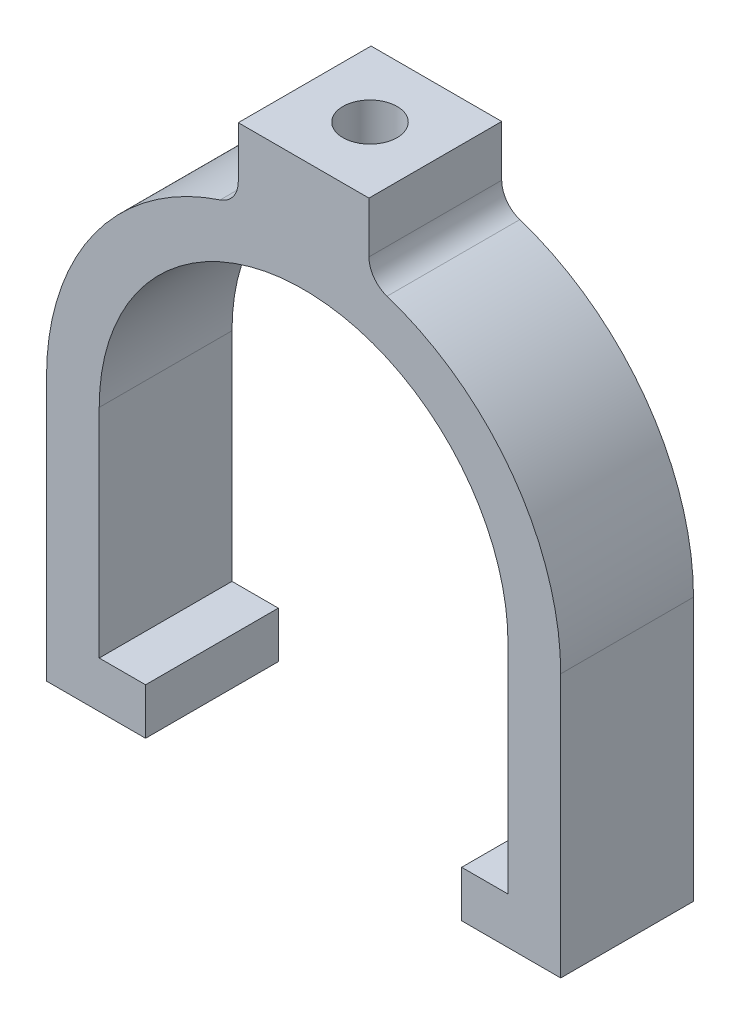
SolidWorks part; units mm, degrees
ref_plane "Front Plane" through (0, 0, 0) normal (0, 0, 1) x (1, 0, 0)
ref_plane "Top Plane" through (0, 0, 0) normal (0, 1, 0) x (1, 0, 0)
ref_plane "Right Plane" through (0, 0, 0) normal (1, 0, 0) x (0, 0, -1)
sketch "Sketch2" plane through (0, 0, 0) normal (0, 0, 1) x (1, 0, 0)
  line L0 (-24.6349, 0) -> (-24.6349, -26.162)
  line L1 (-24.6349, -26.162) -> (-19.05, -26.162)
  line L2 (-19.05, -26.162) -> (-19.05, -31.75)
  line L3 (-19.05, -31.75) -> (-30.988, -31.75)
  line L4 (-30.988, -31.75) -> (-30.988, 0)
  line L11 (24.6349, -26.162) -> (24.6349, 0)
  line L12 (-7.874, 38.1) -> (7.874, 38.1)
  line L13 (7.874, 38.1) -> (7.874, 29.5766)
  line L14 (24.6349, -26.162) -> (19.05, -26.162)
  line L15 (19.05, -26.162) -> (19.05, -31.75)
  line L16 (19.05, -31.75) -> (30.988, -31.75)
  line L18 (30.988, -31.75) -> (30.988, 0)
  line L19 (-7.874, 38.1) -> (-7.874, 29.5766)
  line L20 (0, 0) -> (0, 24.6349) construction
  arc A0 (-24.6349, 0) -> (24.6349, 0) centre (0, 0) cw
  arc A2 (-7.874, 29.5766) -> (-30.988, 0) centre (-0.508, 0) ccw
  arc A3 (30.988, 0) -> (7.874, 29.5766) centre (0.508, 0) ccw
  point P10 (-19.05, -28.956)
  point P21 (0, 0)
  point P22 (0, 0)
  point P23 (0, 0)
  point P24 (31.1506, 1.8704)
  point P25 (0, 0)
  point P26 (-30.4709, -2.1031)
  point P27 (0, 0)
  point P28 (0, 0)
  point P29 (7.874, 27.8152)
  point P30 (32.0856, 1.4667)
  point P31 (0, 0)
  point P32 (0, 0)
  dimension "D1" = 24.6349
  dimension "D2" = 5.588
  dimension "D3" = 15.748
  dimension "D8" = 30.48
  dimension "D9" = 30.48
  dimension "D4" = 31.75
  dimension "D5" = 11.938
  dimension "D6" = 50.038
  dimension "D7" = 61.976
  dimension "D10" = 69.85
extrude "Boss-Extrude1" add sketch "Sketch2" along normal blind 16.002
fillet "Fillet1" radius 3.175 2 edges at (-7.874, 29.5766, 8.001) (7.874, 29.5766, 8.001)
hole_wizard "5/16-18 Tapped Hole1" positions "Sketch3" profile "Sketch4" tap size "5/16-18" standard "ANSI Inch"
sketch "Sketch3" plane through (0, 38.1, 0) normal (0, 1, 0) x (1, 0, 0)
  line L2 (0, 0) -> (0, -16.002)
  line L3 (7.874, -16.002) -> (-7.874, -16.002) construction
  point P24 (0, -8.001)
sketch "Sketch4" plane through (0, 38.1, 8.001) normal (1, 0, 0) x (0, 0, 1)
  line L0 (0, 0) -> (0, 13.4651)
  line L1 (0, 13.4651) -> (3.2639, 13.4651)
  line L2 (3.2639, 13.4651) -> (3.2639, 0)
  line L5 (3.2639, 0) -> (0, 0)
  line L11 (0, -6.35) -> (0, 107.95) construction
  dimension "Thru Tap Drill Dia." = 6.5278
  dimension "Thru Tap Drill Depth" = 13.4651
cosmetic thread "Hole Thread1" parameters "D2"=7.9375
